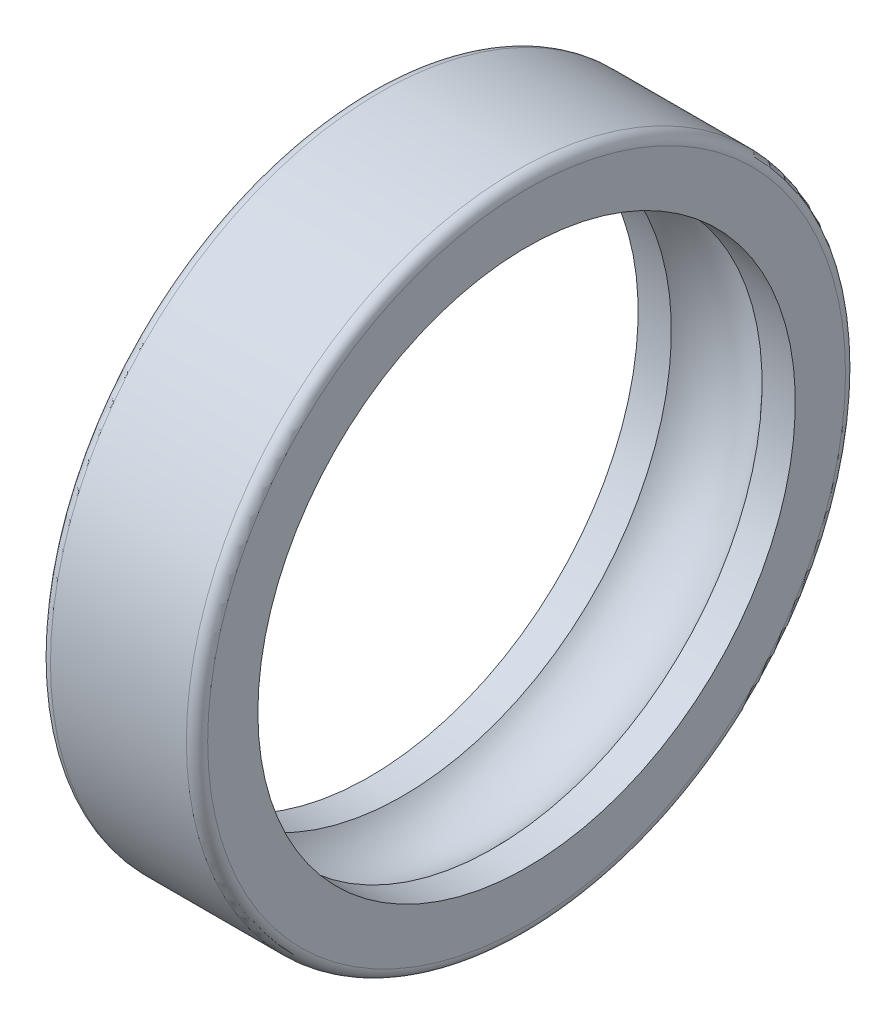
SolidWorks part; units mm, degrees
ref_plane "Front Plane" through (0, 0, 0) normal (0, 0, 1) x (1, 0, 0)
ref_plane "Top Plane" through (0, 0, 0) normal (0, 1, 0) x (1, 0, 0)
ref_plane "Right Plane" through (0, 0, 0) normal (1, 0, 0) x (0, 0, -1)
sketch "Sketch1" plane through (0, 0, 0) normal (0, 0, 1) x (1, 0, 0)
  line L0 (-15.5, 0) -> (43.4408, 0) construction
  line L1 (0, 53) -> (0, 0) construction
  line L2 (8.9443, 53) -> (15.5, 53)
  line L3 (-15.5, 65) -> (15.5, 65)
  line L4 (-15.5, 65) -> (-15.5, 53)
  line L5 (-15.5, 53) -> (-8.9443, 53)
  line L6 (15.5, 65) -> (15.5, 53)
  line L7 (-15.5, 65) -> (15.5, 53) construction
  line L8 (-15.5, 53) -> (15.5, 65) construction
  arc A0 (-8.9443, 53) -> (8.9443, 53) centre (0, 45) cw
  point P3 (0, 59)
  dimension "D5" = 12
  dimension "D1" = 31
  dimension "D2" = 53
  dimension "D3" = 65
  dimension "D4" = 8
revolve "Revolve1" add sketch "Sketch1" angle 360 about L0
fillet "Fillet1" radius 2.1 2 edges at (15.5, 0, 65) (-15.5, 0, 65)
